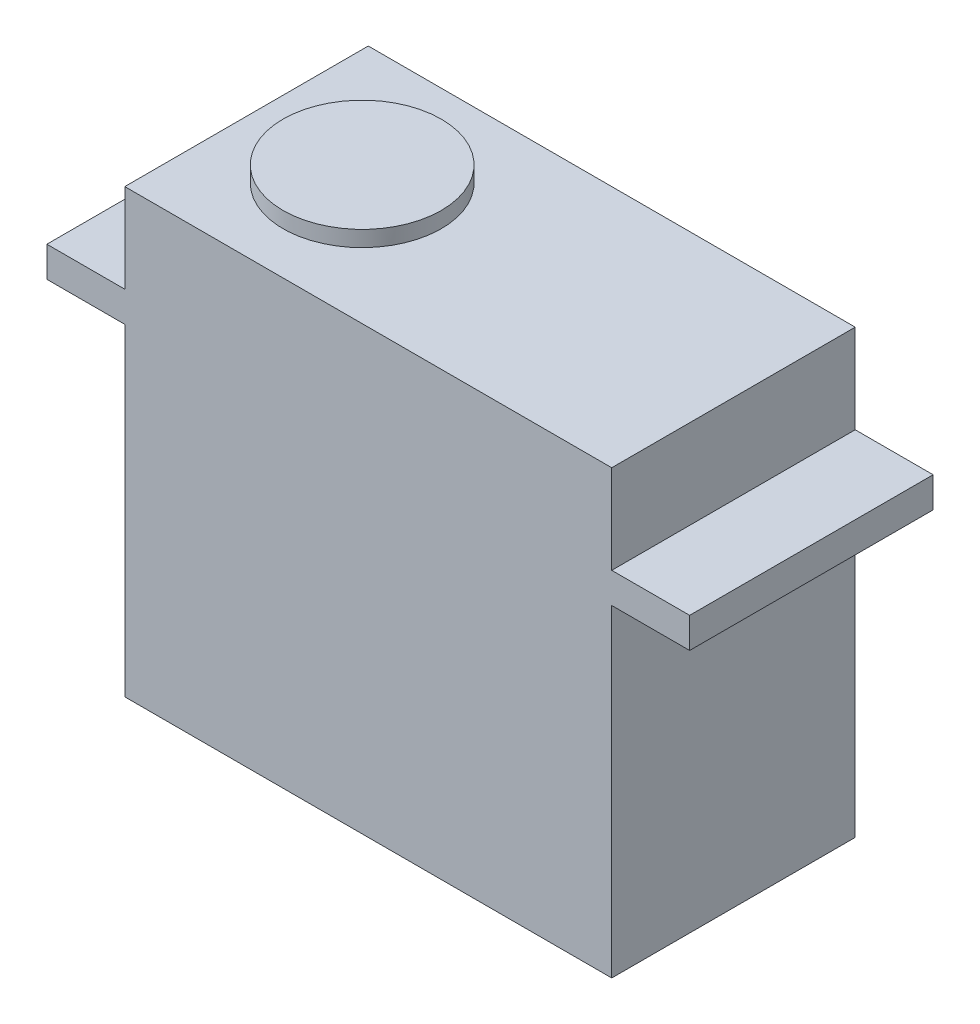
SolidWorks part; units mm, degrees
ref_plane "Front Plane" through (0, 0, 0) normal (0, 0, 1) x (1, 0, 0)
ref_plane "Top Plane" through (0, 0, 0) normal (0, 1, 0) x (1, 0, 0)
ref_plane "Right Plane" through (0, 0, 0) normal (1, 0, 0) x (0, 0, -1)
sketch "Sketch1" plane through (0, 0, 0) normal (0, 1, 0) x (1, 0, 0)
  line L1 (-20, -10) -> (20, -10)
  line L2 (-20, -10) -> (-20, 10)
  line L3 (-20, 10) -> (20, 10)
  line L4 (20, -10) -> (20, 10)
  line L5 (-20, -10) -> (20, 10) construction
  line L6 (-20, 10) -> (20, -10) construction
  point P0 (0, 0)
  dimension "D1" = 40
  dimension "D2" = 20
extrude "Boss-Extrude1" add sketch "Sketch1" along normal blind 26.5
sketch "Sketch2" plane through (0, 26.5, 0) normal (0, 1, 0) x (1, 0, 0)
  line L1 (-26.4, -10) -> (26.4, -10)
  line L2 (-26.4, -10) -> (-26.4, 10)
  line L3 (-26.4, 10) -> (26.4, 10)
  line L4 (26.4, -10) -> (26.4, 10)
  line L5 (-26.4, -10) -> (26.4, 10) construction
  line L6 (-26.4, 10) -> (26.4, -10) construction
  point P0 (0, 0)
  dimension "D1" = 20
  dimension "D2" = 52.8
extrude "Boss-Extrude2" add sketch "Sketch2" along normal blind 2.5
sketch "Sketch3" plane through (0, 29, 0) normal (0, 1, 0) x (1, 0, 0)
  line L0 (26.4, 10) -> (-26.4, 10) construction
  line L1 (-20, -10) -> (20, -10)
  line L2 (-20, -10) -> (-20, 10)
  line L3 (-20, 10) -> (20, 10)
  line L4 (20, -10) -> (20, 10)
  line L5 (-20, -10) -> (20, 10) construction
  line L6 (-20, 10) -> (20, -10) construction
  point P0 (0, 0)
  dimension "D1" = 40
extrude "Boss-Extrude3" add sketch "Sketch3" along normal blind 7.3
sketch "Sketch4" plane through (0, 36.3, 0) normal (0, 1, 0) x (1, 0, 0)
  line L0 (0, 0) -> (-10.5, 0) construction
  line L1 (-20, 10) -> (-20, -10) construction
  circle A0 centre (-10.5, 0) radius 6.5
  dimension "D1" = 13
  dimension "D2" = 9.5
extrude "Boss-Extrude4" add sketch "Sketch4" along normal blind 1.3
